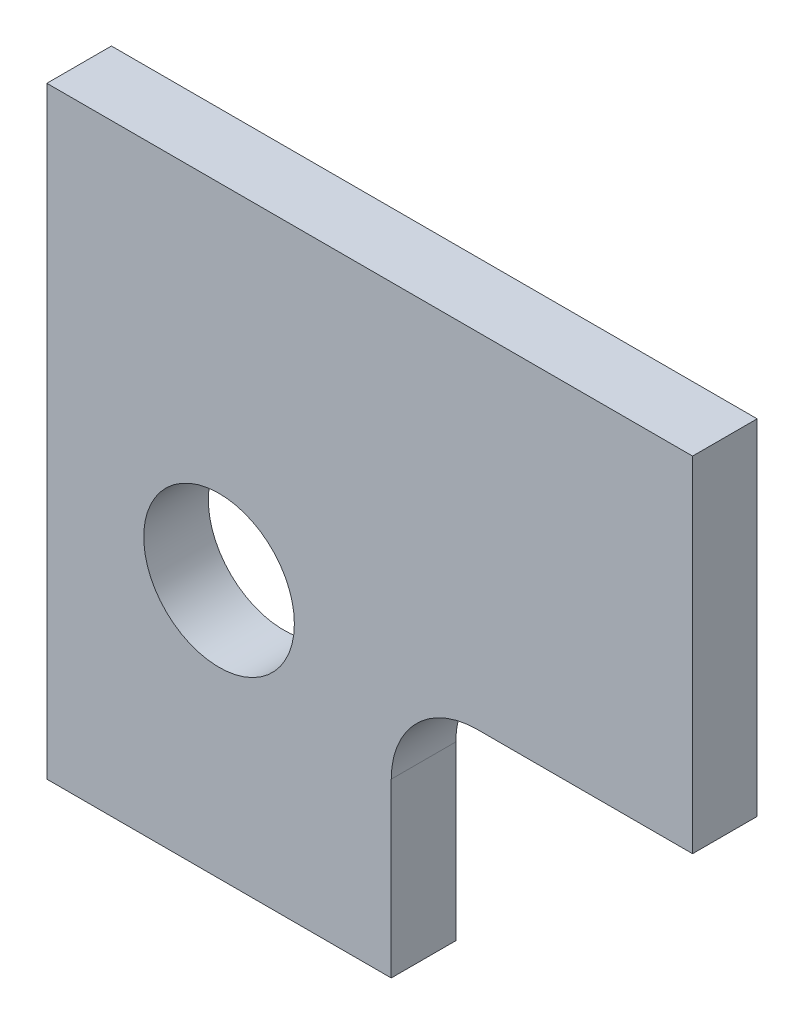
SolidWorks part; units mm, degrees
material "6061-T6 (SS)"
ref_plane "Front Plane" through (0, 0, 0) normal (0, 0, 1) x (1, 0, 0)
ref_plane "Top Plane" through (0, 0, 0) normal (0, 1, 0) x (1, 0, 0)
ref_plane "Right Plane" through (0, 0, 0) normal (1, 0, 0) x (0, 0, -1)
sketch "Sketch1" plane through (0, 0, 0) normal (0, 0, 1) x (1, 0, 0)
  line L0 (4, -6) -> (-4, -6)
  line L1 (-4, -6) -> (-4, 8)
  line L2 (-4, 8) -> (11, 8)
  line L3 (11, 8) -> (11, 0)
  line L4 (11, 0) -> (6, 0)
  line L5 (4, -2) -> (4, -6)
  circle A0 centre (0, 0) radius 1.75
  arc A1 (6, 0) -> (4, -2) centre (6, -2) ccw
  dimension "D3" = 3.5
  dimension "D8" = 2
  dimension "D1" = 8
  dimension "D2" = 4
  dimension "D4" = 6
  dimension "D5" = 14
  dimension "D6" = 15
  dimension "D7" = 8
extrude "Boss-Extrude1" add sketch "Sketch1" along normal blind 1.5
